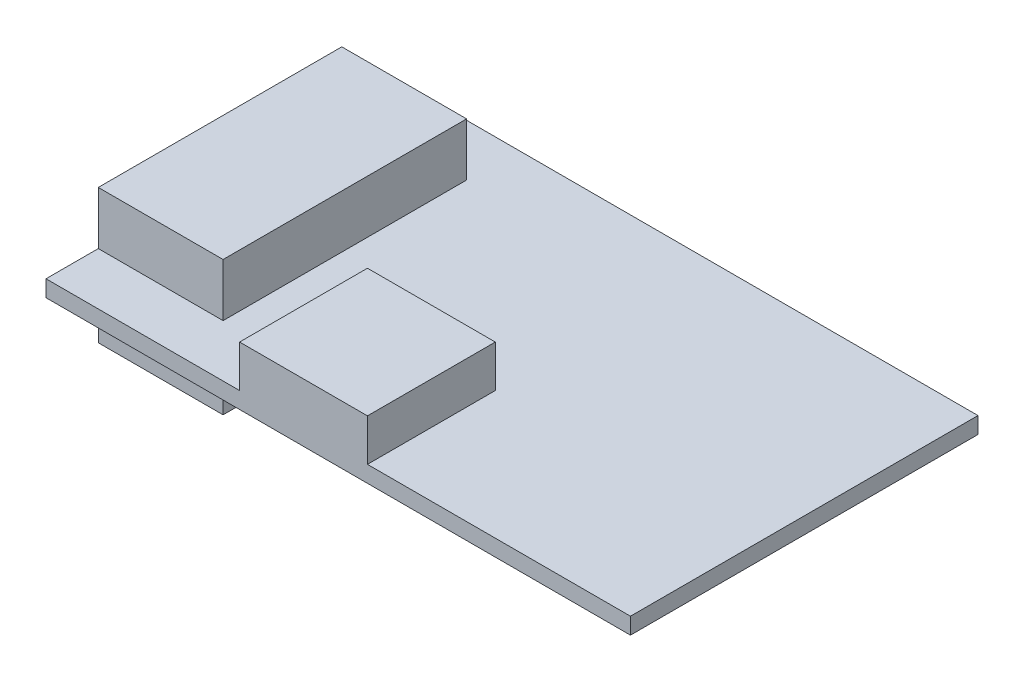
SolidWorks part; units mm, degrees
ref_plane "Front Plane" through (0, 0, 0) normal (0, 0, 1) x (1, 0, 0)
ref_plane "Top Plane" through (0, 0, 0) normal (0, 1, 0) x (1, 0, 0)
ref_plane "Right Plane" through (0, 0, 0) normal (1, 0, 0) x (0, 0, -1)
sketch "Sketch1" plane through (0, 0, 0) normal (0, 1, 0) x (1, 0, 0)
  line L1 (0, 0) -> (24.384, 0)
  line L2 (0, 0) -> (0, 14.5)
  line L3 (0, 14.5) -> (24.384, 14.5)
  line L4 (24.384, 0) -> (24.384, 14.5)
  dimension "D1" = 24.384
  dimension "D2" = 14.5
extrude "Boss-Extrude1" add sketch "Sketch1" along normal blind 0.6858
sketch "Sketch2" plane through (0, 0.6858, 0) normal (0, 1, 0) x (1, 0, 0)
  line L0 (0, 14.5) -> (0, 0) construction
  line L1 (0, 12.341) -> (5.207, 12.341)
  line L2 (0, 12.341) -> (0, 2.181)
  line L3 (0, 2.181) -> (5.207, 2.181)
  line L4 (5.207, 12.341) -> (5.207, 2.181)
  line L6 (24.384, 14.5) -> (0, 14.5) construction
  dimension "D1" = 10.16
  dimension "D2" = 5.207
  dimension "D3" = 0
  dimension "D4" = 2.159
extrude "Boss-Extrude2" add sketch "Sketch2" along normal blind 2.2098
sketch "Sketch3" plane through (0, 0, 0) normal (0, -1, 0) x (1, 0, 0)
  line L0 (0, -14.5) -> (0, 0) construction
  line L1 (0, -2.181) -> (5.207, -2.181)
  line L2 (0, -2.181) -> (0, -12.341)
  line L3 (0, -12.341) -> (5.207, -12.341)
  line L4 (5.207, -2.181) -> (5.207, -12.341)
  line L5 (24.384, -14.5) -> (0, -14.5) construction
  dimension "D1" = 10.16
  dimension "D2" = 5.207
  dimension "D3" = 0
  dimension "D4" = 2.159
extrude "Boss-Extrude3" add sketch "Sketch3" along normal blind 2.7178
sketch "Sketch4" plane through (0, 0.6858, 0) normal (0, 1, 0) x (1, 0, 0)
  line L0 (0, 0) -> (24.384, 0) construction
  line L1 (8.0772, 5.334) -> (13.4112, 5.334)
  line L2 (8.0772, 5.334) -> (8.0772, 0)
  line L3 (8.0772, 0) -> (13.4112, 0)
  line L4 (13.4112, 5.334) -> (13.4112, 0)
  line L5 (0, 2.181) -> (0, 0) construction
  dimension "D1" = 5.334
  dimension "D2" = 5.334
  dimension "D3" = 0
  dimension "D4" = 8.0772
extrude "Boss-Extrude4" add sketch "Sketch4" along normal blind 1.7526
